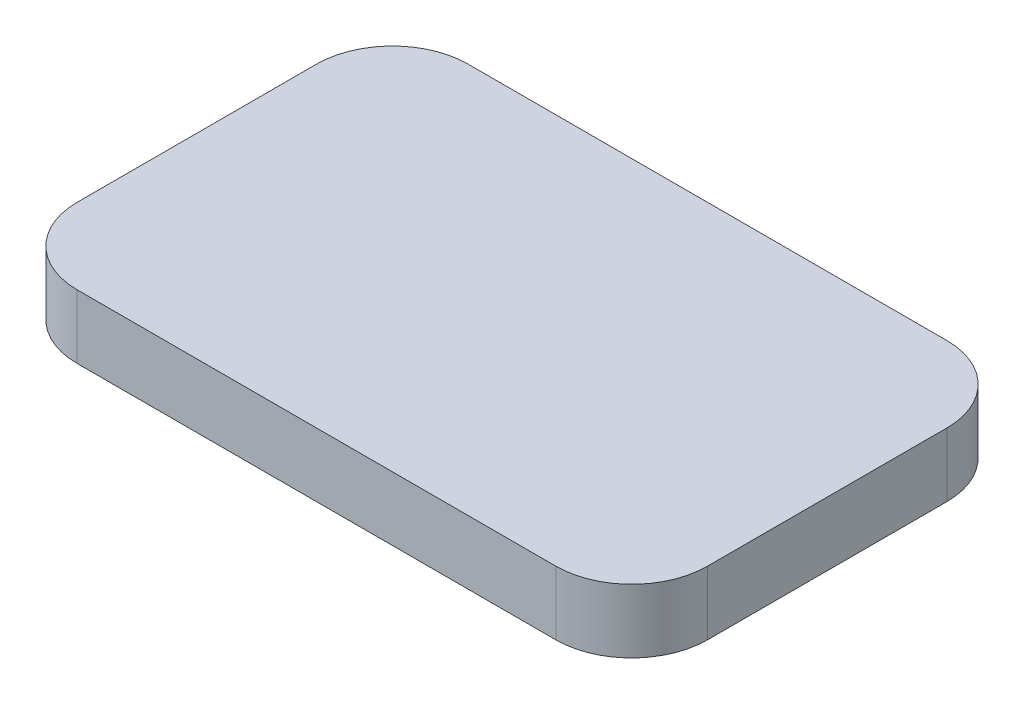
SolidWorks part; units mm, degrees
material "FR4_stuffedProtoboard"
ref_plane "Front Plane" through (0, 0, 0) normal (0, 0, 1) x (1, 0, 0)
ref_plane "Top Plane" through (0, 0, 0) normal (0, 1, 0) x (1, 0, 0)
ref_plane "Right Plane" through (0, 0, 0) normal (1, 0, 0) x (0, 0, -1)
sketch "Sketch1" plane through (0, 0, 0) normal (0, 1, 0) x (1, 0, 0)
  line L1 (-8, -8) -> (8, -8)
  line L2 (-8, -8) -> (-8, 8)
  line L3 (-8, 8) -> (8, 8)
  line L4 (8, -8) -> (8, 8)
  line L5 (-8, -8) -> (8, 8) construction
  line L6 (-8, 8) -> (8, -8) construction
  point P0 (0, 0)
  dimension "D1" = 16
extrude "Boss-Extrude1" add sketch "Sketch1" along normal blind 1.6
sketch "Sketch2" plane through (0, 1.6, 0) normal (0, 1, 0) x (1, 0, 0)
  line L0 (6.0045, 6.15) -> (-5.9955, 6.15)
  line L1 (6.0045, 6.25) -> (-5.9955, 6.25) construction
  line L2 (-7.9955, 4.25) -> (-7.9955, -1.75) construction
  line L3 (-5.9955, -3.75) -> (6.0045, -3.75) construction
  line L4 (8.0045, -1.75) -> (8.0045, 4.25) construction
  line L5 (6.0045, 6.25) -> (-5.9955, 6.25) construction
  line L6 (-7.9955, 4.25) -> (-7.9955, -1.75) construction
  line L7 (-5.9955, -3.75) -> (6.0045, -3.75) construction
  line L8 (8.0045, -1.75) -> (8.0045, 4.25) construction
  line L9 (-7.8955, 4.25) -> (-7.8955, -1.75)
  line L10 (-5.9955, -3.65) -> (6.0045, -3.65)
  line L11 (7.9045, -1.75) -> (7.9045, 4.25)
  arc A0 (8.0045, 4.25) -> (6.0045, 6.25) centre (6.0045, 4.25) ccw construction
  arc A1 (-5.9955, 6.25) -> (-7.9955, 4.25) centre (-5.9955, 4.25) ccw construction
  arc A2 (-7.9955, -1.75) -> (-5.9955, -3.75) centre (-5.9955, -1.75) ccw construction
  arc A3 (6.0045, -3.75) -> (8.0045, -1.75) centre (6.0045, -1.75) ccw construction
  arc A4 (8.0045, 4.25) -> (6.0045, 6.25) centre (6.0045, 4.25) ccw construction
  arc A5 (-5.9955, 6.25) -> (-7.9955, 4.25) centre (-5.9955, 4.25) ccw construction
  arc A6 (-7.9955, -1.75) -> (-5.9955, -3.75) centre (-5.9955, -1.75) ccw construction
  arc A7 (6.0045, -3.75) -> (8.0045, -1.75) centre (6.0045, -1.75) ccw construction
  arc A8 (-5.9955, 6.15) -> (-7.8955, 4.25) centre (-5.9955, 4.25) ccw
  arc A9 (-7.8955, -1.75) -> (-5.9955, -3.65) centre (-5.9955, -1.75) ccw
  arc A10 (6.0045, -3.65) -> (7.9045, -1.75) centre (6.0045, -1.75) ccw
  arc A11 (7.9045, 4.25) -> (6.0045, 6.15) centre (6.0045, 4.25) ccw
  dimension "D1" = 0.1
extrude "Cut-Extrude1" cut sketch "Sketch2" against normal blind 1.6 flip side to cut
sketch "Sketch3" plane through (0, 1.6, 0) normal (0, 1, 0) x (1, 0, 0)
  line L0 (6.525, -1.55) -> (6.525, 1.55) construction
  line L1 (-6.525, -1.55) -> (6.525, -1.55) construction
  line L2 (6.525, 1.55) -> (-6.525, 1.55) construction
  line L3 (-6.525, -1.55) -> (-6.525, 1.55) construction
  line L4 (6.525, -1.55) -> (6.525, 1.55)
  line L5 (-6.525, -1.55) -> (6.525, -1.55)
  line L6 (6.525, 1.55) -> (-6.525, 1.55)
  line L7 (-6.525, -1.55) -> (-6.525, 1.55)
  line L8 (-6.525, 1.55) -> (6.525, -1.55) construction
  line L9 (-6.525, -1.55) -> (6.525, 1.55) construction
  circle A0 centre (0, 0) radius 0.5
  dimension "D1" = 1
